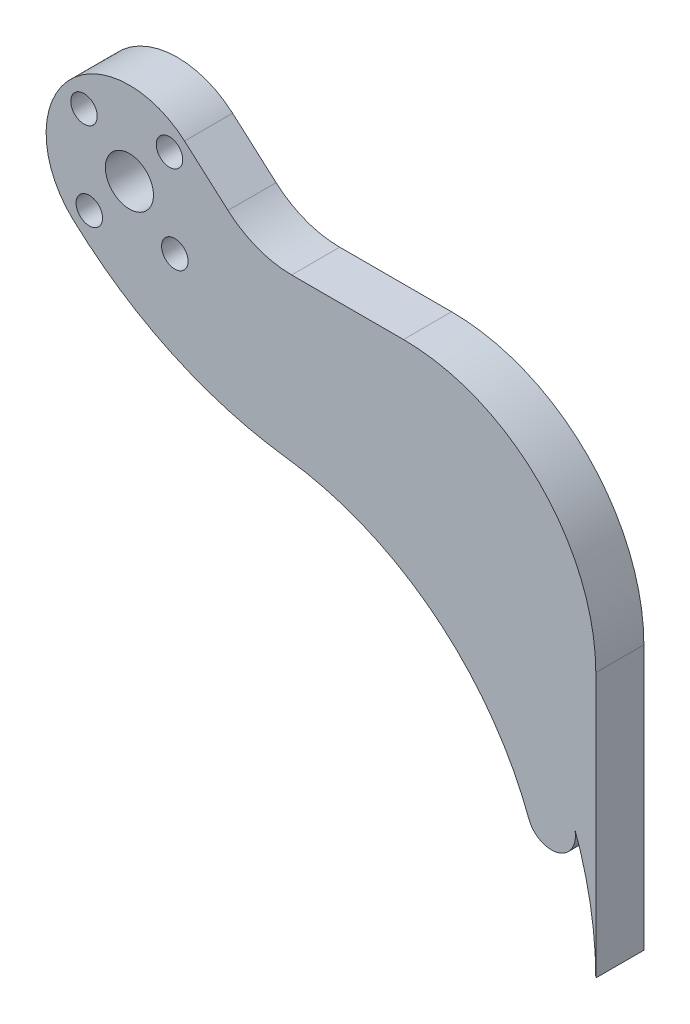
SolidWorks part; units mm, degrees
material "Plain Carbon Steel"
ref_plane "Front Plane" through (0, 0, 0) normal (0, 0, 1) x (1, 0, 0)
ref_plane "Top Plane" through (0, 0, 0) normal (0, 1, 0) x (1, 0, 0)
ref_plane "Right Plane" through (0, 0, 0) normal (1, 0, 0) x (0, 0, -1)
sketch "Sketch1" plane through (0, 0, 0) normal (0, 0, 1) x (1, 0, 0)
  line L2 (-15.875, 60.325) -> (0, 0) construction
  line L3 (-15.875, 60.325) -> (19.685, 60.325) construction
  line L4 (-8.5955, 68.5717) -> (30.2564, 34.2763)
  line L5 (0, 0) -> (3.2321, -12.2818) construction
  arc A0 (36.8803, 13.7783) -> (4.9037, 39.0634) centre (0, 0) ccw
  arc A1 (-23.3666, 52.2704) -> (-8.5955, 68.5717) centre (-15.875, 60.325) cw
  arc A2 (-23.3666, 52.2704) -> (4.9037, 39.0634) centre (11.231, 89.4678) ccw
  arc A4 (36.8803, 13.7783) -> (42.8287, 16.0006) centre (39.8545, 14.8895) ccw
  arc A5 (42.8287, 16.0006) -> (30.2564, 34.2763) centre (0, 0) ccw
  circle A6 centre (-15.875, 60.325) radius 75.0789 construction
  point P0 (-15.875, 60.325)
  dimension "D3" = 11
  dimension "D4" = 39.37
  dimension "D5" = 6.35
  dimension "D7" = 50.8
  dimension "D8" = 12.7
  dimension "D6" = 35.56
extrude "Boss-Extrude1" add sketch "Sketch1" along normal blind 6.35
sketch "Sketch2" plane through (0, 0, 6.35) normal (0, 0, 1) x (1, 0, 0)
  line L0 (-15.875, 60.325) -> (-10.5808, 66.3226) construction
  line L1 (30.2564, 34.2763) -> (-8.5955, 68.5717) construction
  circle A0 centre (-15.875, 60.325) radius 3.175
  circle A1 centre (-10.5808, 66.3226) radius 1.75
  circle A2 centre (-9.8774, 55.0308) radius 1.75
  circle A3 centre (-21.1692, 54.3274) radius 1.75
  circle A4 centre (-21.8726, 65.6192) radius 1.75
  point P16 (-15.875, 60.325)
  dimension "D2" = 3.5
  dimension "D3" = 6.35
  dimension "D1" = 8
  dimension "D4" = 4
extrude "Cut-Extrude1" cut sketch "Sketch2" against normal through all
sketch "Sketch3" plane through (0, 0, 0) normal (0, 0, -1) x (-1, 0, 0)
  line L0 (-0.7469, 60.325) -> (-45.72, 60.325)
  line L1 (-30.2564, 34.2763) -> (8.5955, 68.5717) construction
  line L2 (-45.72, 60.325) -> (-45.72, 0)
  line L3 (-30.2564, 34.2763) -> (-0.7469, 60.325)
  arc A0 (-30.2564, 34.2763) -> (-42.8287, 16.0006) centre (0, 0) ccw construction
  arc A1 (-45.72, 0) -> (-30.2564, 34.2763) centre (0, 0) cw
  point P8 (15.875, 60.325)
extrude "Boss-Extrude2" add sketch "Sketch3" against normal through all
fillet "Fillet1" radius 12.7 1 edges at (0.7469, 60.325, 3.175)
fillet "Fillet2" radius 25.4 1 edges at (45.72, 60.325, 3.175)
